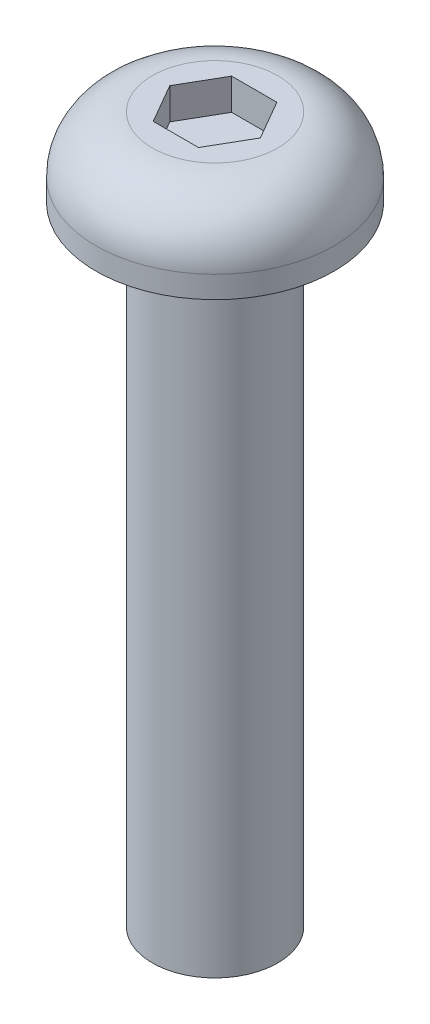
SolidWorks part; units mm, degrees
ref_plane "Front Plane" through (0, 0, 0) normal (0, 0, 1) x (1, 0, 0)
ref_plane "Top Plane" through (0, 0, 0) normal (0, 1, 0) x (1, 0, 0)
ref_plane "Right Plane" through (0, 0, 0) normal (1, 0, 0) x (0, 0, -1)
sketch "Sketch1" plane through (0, 0, 0) normal (0, 0, 1) x (1, 0, 0)
  line L0 (2, 0) -> (3.8, 0)
  line L1 (3.8, 0) -> (3.8, 0.7)
  line L2 (2, 2.5) -> (0, 2.5)
  line L3 (2, 0) -> (2, -20)
  line L4 (2, -20) -> (0, -20)
  line L5 (0, -20) -> (0, 2.5)
  arc A0 (3.8, 0.7) -> (2, 2.5) centre (2, 0.7) ccw
  dimension "D1" = 2
  dimension "D2" = 20
  dimension "D3" = 3.8
  dimension "D4" = 2.5
revolve "Revolve1" add sketch "Sketch1" angle 360 about L5
sketch "Sketch2" plane through (0, 2.5, 0) normal (0, 1, 0) x (1, 0, 0)
  line L1 (0.7217, 1.25) -> (-0.7217, 1.25)
  line L2 (-0.7217, 1.25) -> (-1.4434, 0)
  line L3 (-1.4434, 0) -> (-0.7217, -1.25)
  line L4 (-0.7217, -1.25) -> (0.7217, -1.25)
  line L5 (0.7217, -1.25) -> (1.4434, 0)
  line L6 (1.4434, 0) -> (0.7217, 1.25)
  circle A0 centre (0, 0) radius 1.25 construction
  dimension "D1" = 2.5
extrude "Cut-Extrude1" cut sketch "Sketch2" against normal blind 1
